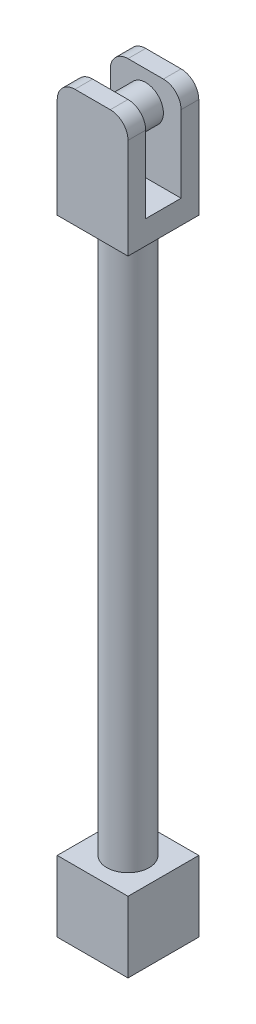
SolidWorks part; units mm, degrees
ref_plane "Front Plane" through (0, 0, 0) normal (0, 0, 1) x (1, 0, 0)
ref_plane "Top Plane" through (0, 0, 0) normal (0, 1, 0) x (1, 0, 0)
ref_plane "Right Plane" through (0, 0, 0) normal (1, 0, 0) x (0, 0, -1)
sketch "Sketch1" plane through (0, 0, 0) normal (0, 1, 0) x (1, 0, 0)
  line L1 (-15, 15) -> (15, 15)
  line L2 (-15, 15) -> (-15, -15)
  line L3 (-15, -15) -> (15, -15)
  line L4 (15, 15) -> (15, -15)
  line L5 (-15, 15) -> (15, -15) construction
  line L6 (-15, -15) -> (15, 15) construction
  point P0 (0, 0)
  dimension "D1" = 30
  dimension "D2" = 30
extrude "Boss-Extrude1" add sketch "Sketch1" along normal blind 30
sketch "Sketch2" plane through (0, 30, 0) normal (0, 1, 0) x (1, 0, 0)
  circle A0 centre (0, 0) radius 9
  dimension "D1" = 18
extrude "Boss-Extrude2" add sketch "Sketch2" along normal blind 235
sketch "Sketch3" plane through (0, 265, 0) normal (0, 1, 0) x (1, 0, 0)
  line L1 (-15, 15) -> (15, 15)
  line L2 (-15, 15) -> (-15, -15)
  line L3 (-15, -15) -> (15, -15)
  line L4 (15, 15) -> (15, -15)
  line L5 (-15, 15) -> (15, -15) construction
  line L6 (-15, -15) -> (15, 15) construction
  point P0 (0, 0)
  dimension "D1" = 30
  dimension "D2" = 30
extrude "Boss-Extrude3" add sketch "Sketch3" along normal blind 50
sketch "Sketch4" plane through (0, 315, 0) normal (0, 1, 0) x (1, 0, 0)
  line L0 (-15, 15) -> (-15, -15) construction
  line L1 (-15, 7.5) -> (15, 7.5)
  line L2 (-15, 7.5) -> (-15, -7.5)
  line L3 (-15, -7.5) -> (15, -7.5)
  line L4 (15, 7.5) -> (15, -7.5)
  line L5 (15, -15) -> (15, 15) construction
  line L6 (-15, -15) -> (15, -15) construction
  dimension "D1" = 15
  dimension "D2" = 7.5
extrude "Cut-Extrude1" cut sketch "Sketch4" against normal blind 40
sketch "Sketch5" plane through (0, 0, 7.5) normal (0, 0, -1) x (-1, 0, 0)
  line L0 (15, 315) -> (-15, 315) construction
  line L1 (15, 275) -> (15, 315) construction
  circle A0 centre (0, 302.5) radius 7.5
  dimension "D1" = 15
  dimension "D2" = 12.5
  dimension "D3" = 15
extrude "Boss-Extrude4" add sketch "Sketch5" along normal up to surface (15 mm away) up to face at (0, 295, -7.5)
fillet "Fillet1" radius 7.5 4 edges at (15, 315, -11.25) (15, 315, 11.25) (-15, 315, 11.25) (-15, 315, -11.25)
